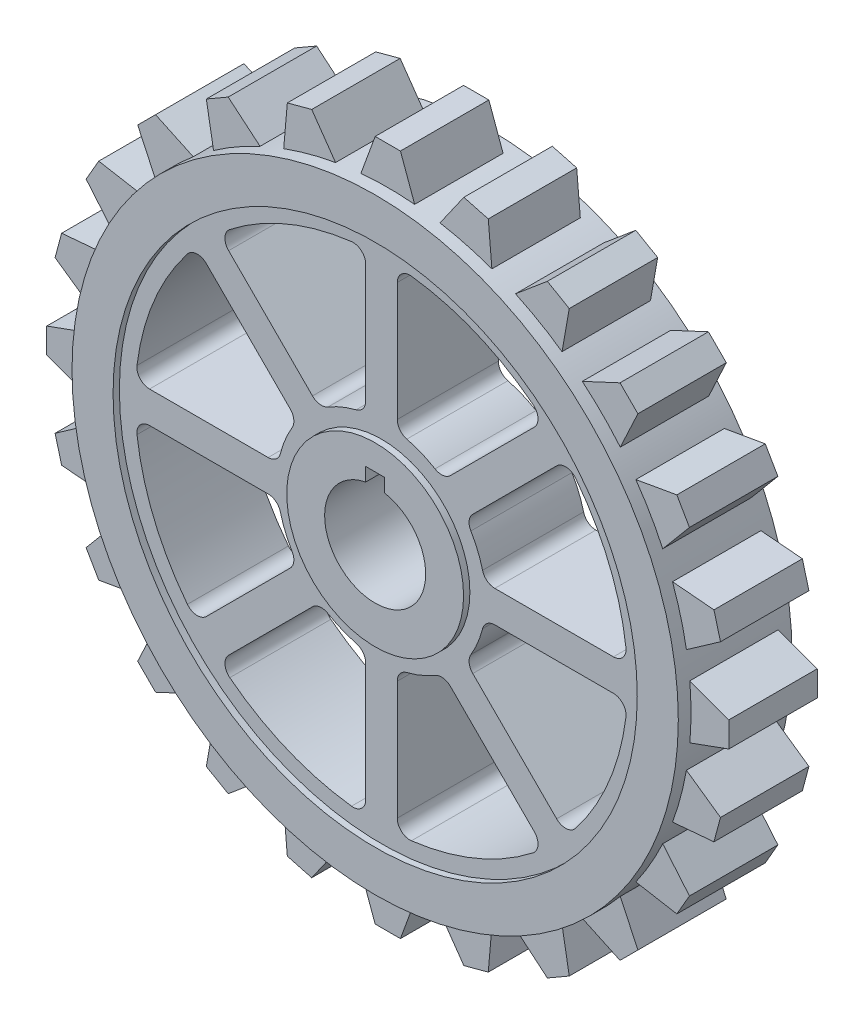
SolidWorks part; units mm, degrees
material "Cast Carbon Steel"
ref_plane "Front Plane" through (0, 0, 0) normal (0, 0, 1) x (1, 0, 0)
ref_plane "Top Plane" through (0, 0, 0) normal (0, 1, 0) x (1, 0, 0)
ref_plane "Right Plane" through (0, 0, 0) normal (1, 0, 0) x (0, 0, -1)
sketch "Sketch1" plane through (0, 0, 0) normal (0, 0, 1) x (1, 0, 0)
  line L0 (0, 0) -> (0, 50000) construction
  line L1 (0, 0) -> (50000, 0) construction
  line L2 (-1.5, 10) -> (-1.5, 7.8581)
  line L3 (1.5, 10) -> (1.5, 7.8581)
  line L4 (-1.5, 10) -> (1.5, 10)
  line L5 (-2.5, 36.7253) -> (-2.5, 17.9444)
  line L6 (2.5, 17.9444) -> (2.5, 36.7253)
  line L7 (24.201, 27.7365) -> (10.9208, 14.4563)
  line L8 (14.4563, 10.9208) -> (27.7365, 24.201)
  line L9 (36.7253, 2.5) -> (17.9444, 2.5)
  line L10 (17.9444, -2.5) -> (36.7253, -2.5)
  line L11 (27.7365, -24.201) -> (14.4563, -10.9208)
  line L12 (10.9208, -14.4563) -> (24.201, -27.7365)
  line L13 (2.5, -36.7253) -> (2.5, -17.9444)
  line L14 (-2.5, -17.9444) -> (-2.5, -36.7253)
  line L15 (-24.201, -27.7365) -> (-10.9208, -14.4563)
  line L16 (-14.4563, -10.9208) -> (-27.7365, -24.201)
  line L17 (-36.7253, -2.5) -> (-17.9444, -2.5)
  line L18 (-17.9444, 2.5) -> (-36.7253, 2.5)
  line L19 (-27.7365, 24.201) -> (-14.4563, 10.9208)
  line L20 (-10.9208, 14.4563) -> (-24.201, 27.7365)
  arc A0 (-1.5, 7.8581) -> (1.5, 7.8581) centre (0, 0) ccw
  circle A2 centre (0, 0) radius 14 construction
  arc A3 (-4.0135, 16.0044) -> (-8.4789, 14.1548) centre (0, 0) ccw
  arc A4 (-4.7432, 38.7105) -> (-24.0185, 30.7264) centre (0, 0) ccw
  circle A5 centre (0, 0) radius 41.5 construction
  circle A6 centre (0, 0) radius 48
  arc A7 (2.5, 17.9444) -> (4.0135, 16.0044) centre (4.5, 17.9444) ccw
  arc A8 (-2.5, 17.9444) -> (-4.0135, 16.0044) centre (-4.5, 17.9444) cw
  arc A9 (2.5, 36.7253) -> (4.7432, 38.7105) centre (4.5, 36.7253) cw
  arc A10 (-2.5, 36.7253) -> (-4.7432, 38.7105) centre (-4.5, 36.7253) ccw
  arc A11 (27.7365, 24.201) -> (30.7264, 24.0185) centre (29.1507, 22.7868) cw
  arc A12 (24.201, 27.7365) -> (24.0185, 30.7264) centre (22.7868, 29.1507) ccw
  arc A13 (10.9208, 14.4563) -> (8.4789, 14.1548) centre (9.5066, 15.8706) cw
  arc A14 (14.4563, 10.9208) -> (14.1548, 8.4789) centre (15.8706, 9.5066) ccw
  arc A15 (36.7253, -2.5) -> (38.7105, -4.7432) centre (36.7253, -4.5) cw
  arc A16 (36.7253, 2.5) -> (38.7105, 4.7432) centre (36.7253, 4.5) ccw
  arc A17 (17.9444, 2.5) -> (16.0044, 4.0135) centre (17.9444, 4.5) cw
  arc A18 (17.9444, -2.5) -> (16.0044, -4.0135) centre (17.9444, -4.5) ccw
  arc A19 (24.201, -27.7365) -> (24.0185, -30.7264) centre (22.7868, -29.1507) cw
  arc A20 (27.7365, -24.201) -> (30.7264, -24.0185) centre (29.1507, -22.7868) ccw
  arc A21 (14.4563, -10.9208) -> (14.1548, -8.4789) centre (15.8706, -9.5066) cw
  arc A22 (10.9208, -14.4563) -> (8.4789, -14.1548) centre (9.5066, -15.8706) ccw
  arc A23 (-2.5, -36.7253) -> (-4.7432, -38.7105) centre (-4.5, -36.7253) cw
  arc A24 (2.5, -36.7253) -> (4.7432, -38.7105) centre (4.5, -36.7253) ccw
  arc A25 (2.5, -17.9444) -> (4.0135, -16.0044) centre (4.5, -17.9444) cw
  arc A26 (-2.5, -17.9444) -> (-4.0135, -16.0044) centre (-4.5, -17.9444) ccw
  arc A27 (-27.7365, -24.201) -> (-30.7264, -24.0185) centre (-29.1507, -22.7868) cw
  arc A28 (-24.201, -27.7365) -> (-24.0185, -30.7264) centre (-22.7868, -29.1507) ccw
  arc A29 (-10.9208, -14.4563) -> (-8.4789, -14.1548) centre (-9.5066, -15.8706) cw
  arc A30 (-14.4563, -10.9208) -> (-14.1548, -8.4789) centre (-15.8706, -9.5066) ccw
  arc A31 (-36.7253, 2.5) -> (-38.7105, 4.7432) centre (-36.7253, 4.5) cw
  arc A32 (-36.7253, -2.5) -> (-38.7105, -4.7432) centre (-36.7253, -4.5) ccw
  arc A33 (-17.9444, -2.5) -> (-16.0044, -4.0135) centre (-17.9444, -4.5) cw
  arc A34 (-17.9444, 2.5) -> (-16.0044, 4.0135) centre (-17.9444, 4.5) ccw
  arc A35 (-24.201, 27.7365) -> (-24.0185, 30.7264) centre (-22.7868, 29.1507) cw
  arc A36 (-27.7365, 24.201) -> (-30.7264, 24.0185) centre (-29.1507, 22.7868) ccw
  arc A37 (-14.4563, 10.9208) -> (-14.1548, 8.4789) centre (-15.8706, 9.5066) cw
  arc A38 (-10.9208, 14.4563) -> (-8.4789, 14.1548) centre (-9.5066, 15.8706) ccw
  arc A39 (-30.7264, 24.0185) -> (-38.7105, 4.7432) centre (0, 0) ccw
  arc A40 (-14.1548, 8.4789) -> (-16.0044, 4.0135) centre (0, 0) ccw
  arc A41 (8.4789, 14.1548) -> (4.0135, 16.0044) centre (0, 0) ccw
  arc A42 (24.0185, 30.7264) -> (4.7432, 38.7105) centre (0, 0) ccw
  arc A43 (38.7105, 4.7432) -> (30.7264, 24.0185) centre (0, 0) ccw
  arc A44 (16.0044, 4.0135) -> (14.1548, 8.4789) centre (0, 0) ccw
  arc A45 (-16.0044, -4.0135) -> (-14.1548, -8.4789) centre (0, 0) ccw
  arc A46 (-8.4789, -14.1548) -> (-4.0135, -16.0044) centre (0, 0) ccw
  arc A47 (4.0135, -16.0044) -> (8.4789, -14.1548) centre (0, 0) ccw
  arc A48 (14.1548, -8.4789) -> (16.0044, -4.0135) centre (0, 0) ccw
  arc A49 (-38.7105, -4.7432) -> (-30.7264, -24.0185) centre (0, 0) ccw
  arc A50 (30.7264, -24.0185) -> (38.7105, -4.7432) centre (0, 0) ccw
  arc A51 (-24.0185, -30.7264) -> (-4.7432, -38.7105) centre (0, 0) ccw
  arc A52 (4.7432, -38.7105) -> (24.0185, -30.7264) centre (0, 0) ccw
  point P1 (0, 10)
  point P27 (-4.0135, 16.0044)
  point P28 (16.0044, 4.0135)
  point P112 (0, 0)
  point P113 (-15.8706, -4.0135)
  point P114 (-8.4789, -14.4563)
  dimension "D1" = 16
  dimension "D2" = 28
  dimension "D6" = 96
  dimension "D9" = 2
  dimension "D3" = 2.5
  dimension "D4" = 6.5
  dimension "D5" = 2.5
  dimension "D7" = 3
  dimension "D8" = 10
  dimension "D10" = 5
  dimension "D11" = 8
extrude "Boss-Extrude2" add sketch "Sketch1" along normal mid plane 18
sketch "Sketch2" plane through (0, 0, 9) normal (0, 0, 1) x (1, 0, 0)
  circle A0 centre (0, 0) radius 14
  circle A1 centre (0, 0) radius 41.5
  circle A2 centre (0, 0) radius 48 construction
  dimension "D1" = 28
  dimension "D2" = 6.5
extrude "Cut-Extrude1" cut sketch "Sketch2" against normal blind 1
sketch "Sketch3" plane through (0, 0, -9) normal (0, 0, -1) x (-1, 0, 0)
  circle A0 centre (0, 0) radius 14
  circle A1 centre (0, 0) radius 41.5
  circle A2 centre (0, 0) radius 48 construction
  dimension "D1" = 28
  dimension "D2" = 6.5
extrude "Cut-Extrude2" cut sketch "Sketch3" against normal blind 1
sketch "Sketch4" plane through (0, 0, 0) normal (0, 0, 1) x (1, 0, 0)
  line L0 (-2, 54) -> (2, 54)
  line L1 (2, 54) -> (4.2525, 47.8113)
  line L2 (-2, 54) -> (-4.2525, 47.8113)
  line L3 (0, 0) -> (0, 48) construction
  circle A0 centre (0, 0) radius 48 construction
  arc A25 (4.2525, 47.8113) -> (-4.2525, 47.8113) centre (0, 0) ccw
  point P2 (0, 54)
  point P10 (0, 0)
  dimension "D4" = 6
  dimension "D1" = 4
  dimension "D3" = 40
extrude "Boss-Extrude3" add sketch "Sketch4" along normal mid plane 14
pattern_circular "CirPattern1" count 24 over 360 about axis through (0, 0, 0) along (0, 0, 1) of "Boss-Extrude3"
equation "\"A\" = 108"
equation "\"B\" = 24"
equation "\"C\"= 2.5"
equation "\"D3@Sketch1\"=\"C\""
equation "\"D5@Sketch1\"=\"C\""
equation "\"D6@Sketch1\"=\"A\"-12"
equation "\"D10@Sketch1\"=\"C\"*2"
equation "\"D1@CirPattern1\"=\"B\""
